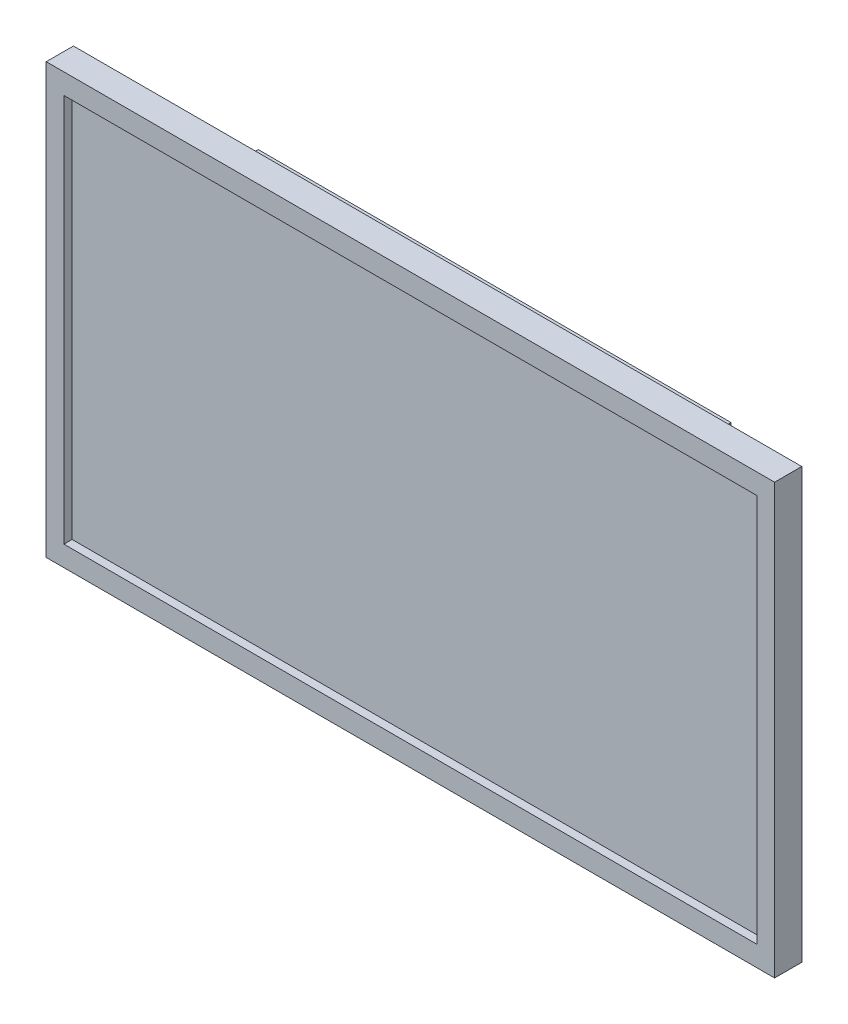
SolidWorks part; units mm, degrees
ref_plane "前视基准面" through (0, 0, 0) normal (0, 0, 1) x (1, 0, 0)
ref_plane "上视基准面" through (0, 0, 0) normal (0, 1, 0) x (1, 0, 0)
ref_plane "右视基准面" through (0, 0, 0) normal (1, 0, 0) x (0, 0, -1)
sketch "草图2" plane through (0, 0, 0) normal (0, 0, 1) x (1, 0, 0)
  line L0 (-134, 79) -> (-134, -79)
  line L1 (-134, -79) -> (134, -79)
  line L2 (134, -79) -> (134, 79)
  line L3 (134, 79) -> (-134, 79)
  line L4 (-134, 0) -> (134, 0) construction
  dimension "D1" = 268
  dimension "D2" = 158
extrude "凸台-拉伸1" add sketch "草图2" against normal blind 10
sketch "草图3" plane through (0, 0, 0) normal (0, 0, 1) x (1, 0, 0)
  line L0 (-87, 59) -> (-87, -59)
  line L1 (-87, -59) -> (87, -59)
  line L2 (87, -59) -> (87, 59)
  line L3 (87, 59) -> (-87, 59)
  line L4 (-87, 0) -> (87, 0) construction
  dimension "D1" = 174
  dimension "D2" = 118
extrude "凸台-拉伸2" add sketch "草图3" against normal blind 31
sketch "草图4" plane through (0, 0, 0) normal (0, 0, 1) x (1, 0, 0)
  line L0 (-127.5, 0) -> (127.5, 0) construction
  line L1 (-127.5, 71.5) -> (127.5, 71.5)
  line L2 (-127.5, 71.5) -> (-127.5, -71.5)
  line L3 (-127.5, -71.5) -> (127.5, -71.5)
  line L4 (127.5, 71.5) -> (127.5, -71.5)
  dimension "D1" = 255
  dimension "D2" = 143
extrude "切除-拉伸1" cut sketch "草图4" against normal blind 3
